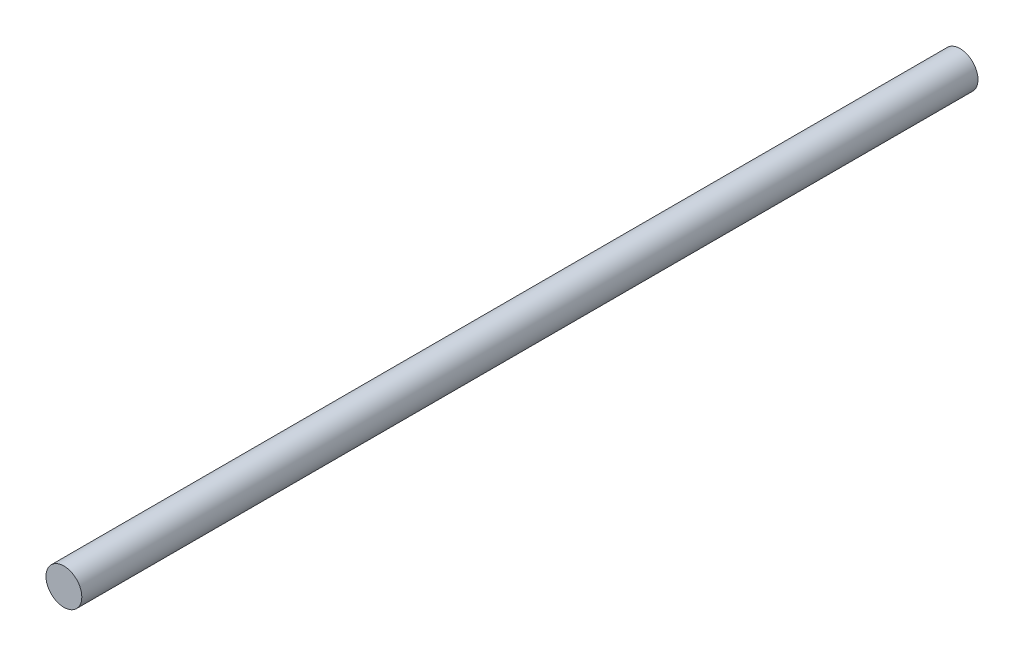
SolidWorks part; units mm, degrees
ref_plane "Alzado" through (0, 0, 0) normal (0, 0, 1) x (1, 0, 0)
ref_plane "Planta" through (0, 0, 0) normal (0, 1, 0) x (1, 0, 0)
ref_plane "Vista lateral" through (0, 0, 0) normal (1, 0, 0) x (0, 0, -1)
sketch "Croquis1" plane through (0, 0, 0) normal (0, 0, 1) x (1, 0, 0)
  circle A0 centre (0, 0) radius 5
  dimension "D1" = 10
extrude "Saliente-Extruir1" add sketch "Croquis1" along normal blind 250
